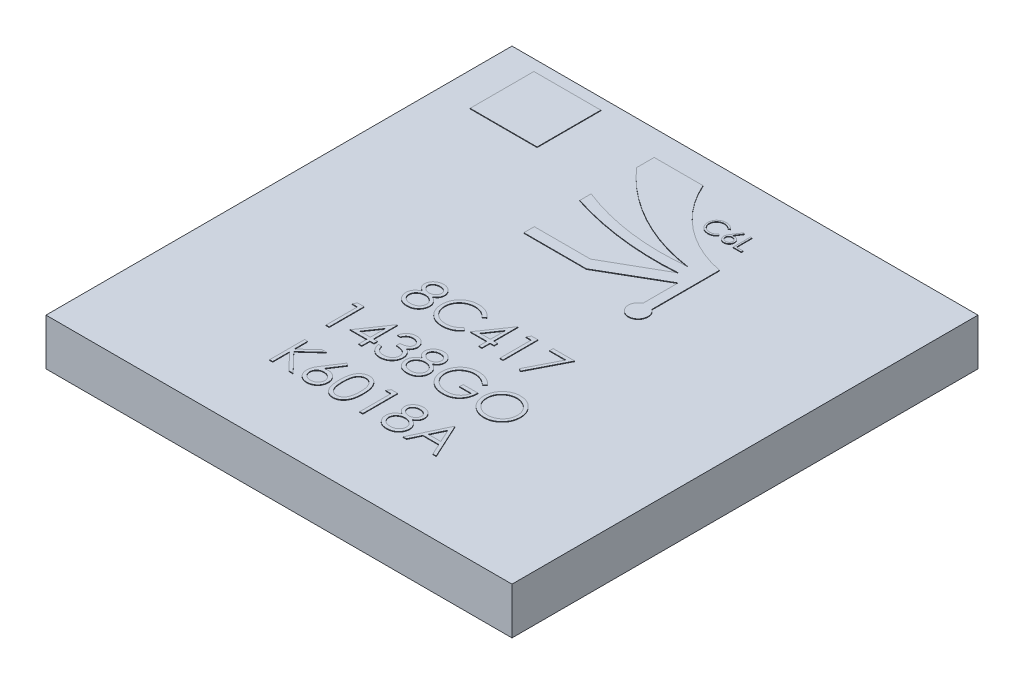
SolidWorks part; units mm, degrees
ref_plane "Plan de face" through (0, 0, 0) normal (0, 0, 1) x (1, 0, 0)
ref_plane "Plan de dessus" through (0, 0, 0) normal (0, 1, 0) x (1, 0, 0)
ref_plane "Plan de droite" through (0, 0, 0) normal (1, 0, 0) x (0, 0, -1)
sketch "Esquisse1" plane through (0, 0, 0) normal (0, 1, 0) x (1, 0, 0)
  line L1 (4, -4) -> (-4, -4)
  line L2 (4, -4) -> (4, 4)
  line L3 (4, 4) -> (-4, 4)
  line L4 (-4, -4) -> (-4, 4)
  line L5 (4, -4) -> (-4, 4) construction
  line L6 (4, 4) -> (-4, -4) construction
  point P0 (0, 0)
  dimension "D1" = 8
  dimension "D2" = 8
extrude "Boss.-Extru.1" add sketch "Esquisse1" along normal blind 0.8
sketch "Esquisse2" plane through (0, 0.8, 0) normal (0, 1, 0) x (1, 0, 0)
  line L0 (0, 2.8971) -> (1.3408, 2.8971) construction
  line L1 (-2.526, -0.7542) -> (2.526, -0.7542) construction
  line L2 (-2.526, -1.7542) -> (2.526, -1.7542) construction
  line L3 (-2.526, -2.7542) -> (2.526, -2.7542) construction
  line L4 (0, 0) -> (0, 1.7957) construction
  text T0 "8C417" font "Century Gothic" height 0.6
  text T1 "1438GO" font "Century Gothic" height 0.6
  text T2 "K6018A" font "Century Gothic" height 0.6
  text T3 "C6L" font "Century Gothic" height 0.3
  dimension "D1" = 1
  dimension "D2" = 1
extrude "Boss.-Extru.2" add sketch "Esquisse2" along normal blind 0.01
sketch "Esquisse3" plane through (0, 0.8, 0) normal (0, 1, 0) x (1, 0, 0)
  line L0 (-1.1134, 2.4723) -> (-1.1134, 2.2761)
  line L1 (-1.1134, 1.4964) -> (-1.1134, 1.3172)
  line L3 (-3.4239, 3.7998) -> (-2.2746, 3.7998)
  line L4 (-3.4239, 3.7998) -> (-3.4239, 2.7056)
  line L5 (-3.4239, 2.7056) -> (-2.2746, 2.7056)
  line L6 (-2.2746, 3.7998) -> (-2.2746, 2.7056)
  line L7 (-3.4239, 3.7998) -> (-2.2746, 2.7056) construction
  line L8 (-3.4239, 2.7056) -> (-2.2746, 3.7998) construction
  line L10 (-1.1134, 1.4964) -> (-0.1498, 1.4964)
  line L11 (-1.1134, 3.5547) -> (-0.2749, 3.5547)
  line L12 (-1.1134, 3.5547) -> (-1.1134, 3.2527)
  line L13 (-1.1134, 1.3172) -> (-0.0416, 1.3172)
  line L14 (1.1253, 2.4378) -> (1.1253, 1.2769)
  line L15 (-1.1134, 3.5547) -> (1.1253, 1.1074) construction
  line L16 (-1.1134, 1.3172) -> (1.1253, 3.5678) construction
  line L17 (-0.1498, 1.4964) -> (0.814, 2.0462)
  line L18 (-0.0416, 1.3172) -> (0.9577, 1.8951)
  line L19 (0.9577, 1.8951) -> (0.9577, 1.2906)
  arc A5 (-1.1134, 3.2527) -> (0.7912, 2.2205) centre (1.2288, 5.3013) ccw
  arc A6 (-0.2749, 3.5547) -> (1.1253, 2.4378) centre (1.4842, 4.3238) ccw
  arc A7 (-1.1134, 2.4723) -> (0.7912, 2.2205) centre (0.3475, 6.1941) ccw
  arc A8 (-1.1134, 2.2761) -> (0.814, 2.0462) centre (0.4462, 7.1568) ccw
  arc A9 (0.9577, 1.2906) -> (1.1253, 1.2769) centre (1.0296, 1.1373) ccw
  point P0 (-2.8492, 3.2527)
  dimension "D12" = 0.3386
extrude "Boss.-Extru.4" add sketch "Esquisse3" along normal blind 0.01
